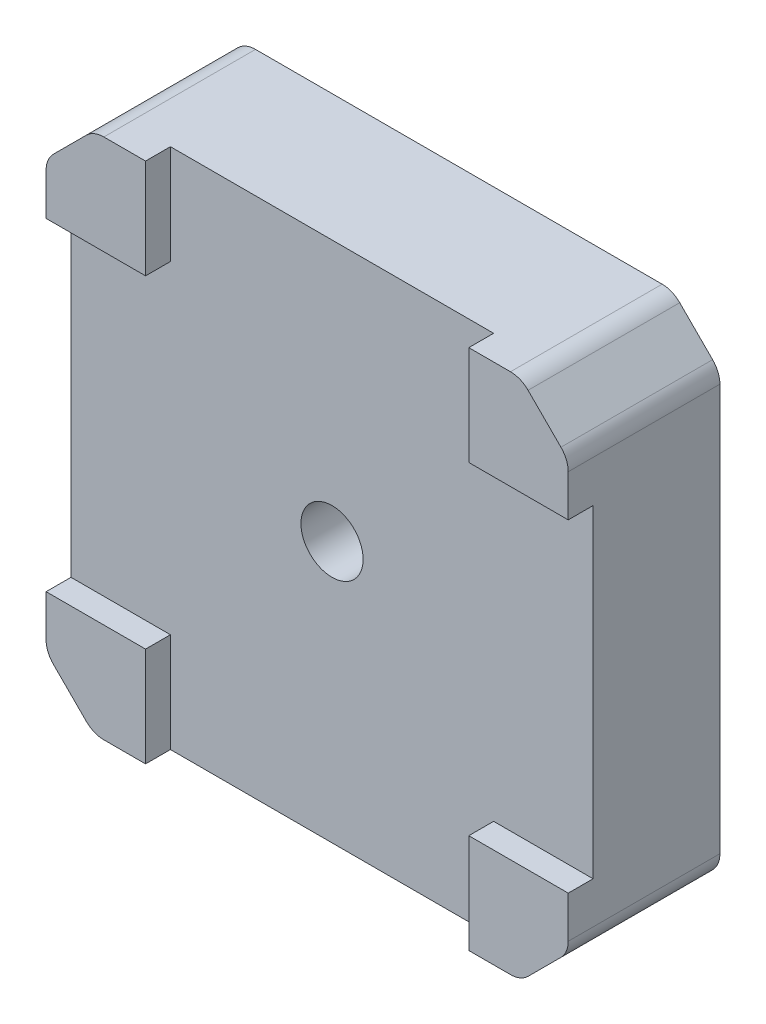
SolidWorks part; units mm, degrees
material "Alumina"
ref_plane "Front" through (0, 0, 0) normal (0, 0, 1) x (1, 0, 0)
ref_plane "Top" through (0, 0, 0) normal (0, 1, 0) x (1, 0, 0)
ref_plane "Right" through (0, 0, 0) normal (1, 0, 0) x (0, 0, -1)
sketch "Sketch1" plane through (0, 0, 0) normal (0, 0, 1) x (1, 0, 0)
  line L0 (-17.1838, 21) -> (-21, 17.1838)
  line L1 (-17.1838, -21) -> (17.1838, -21)
  line L2 (-21, -17.1838) -> (-21, 17.1838)
  line L3 (-17.1838, 21) -> (17.1838, 21)
  line L4 (21, -17.1838) -> (21, 17.1838)
  line L5 (-19.0919, 19.0919) -> (19.0919, -19.0919) construction
  line L6 (19.0919, 19.0919) -> (-19.0919, -19.0919) construction
  line L7 (0, -21) -> (0, 21) construction
  line L8 (-21, 0) -> (21, 0) construction
  line L9 (17.1838, 21) -> (21, 17.1838)
  line L10 (17.1838, -21) -> (21, -17.1838)
  line L11 (-17.1838, -21) -> (-21, -17.1838)
  point P0 (0, 0)
  dimension "D1" = 42
  dimension "D2" = 42
  dimension "D3" = 54
extrude "Boss-Extrude1" add sketch "Sketch1" along normal blind 12.2
sketch "Sketch2" plane through (21, 0, 0) normal (1, 0, 0) x (0, 0, -1)
  line L0 (-12.2, -17.1838) -> (-12.2, 17.1838) construction
  line L1 (-12.2, 13) -> (-10.2, 13)
  line L2 (-12.2, 13) -> (-12.2, -13)
  line L3 (-12.2, -13) -> (-10.2, -13)
  line L4 (-10.2, 13) -> (-10.2, -13)
  line L7 (0, 0) -> (-12.2, 0) construction
  line L8 (0, -17.1838) -> (0, 17.1838) construction
  dimension "D1" = 2
  dimension "D2" = 26
extrude "Cut-Extrude1" cut sketch "Sketch2" against normal through all
sketch "Sketch3" plane through (0, 21, 0) normal (0, 1, 0) x (1, 0, 0)
  line L0 (17.1838, -12.2) -> (-17.1838, -12.2) construction
  line L1 (-13, -12.2) -> (13, -12.2)
  line L2 (-13, -12.2) -> (-13, -10.2)
  line L3 (-13, -10.2) -> (13, -10.2)
  line L4 (13, -12.2) -> (13, -10.2)
  line L7 (0, 0) -> (0, -12.2) construction
  line L8 (17.1838, 0) -> (-17.1838, 0) construction
  dimension "D1" = 2
  dimension "D2" = 26
extrude "Cut-Extrude2" cut sketch "Sketch3" against normal through all
sketch "Sketch4" plane through (0, 0, 0) normal (0, 0, -1) x (-1, 0, 0)
  circle A0 centre (0, 0) radius 16.5
  dimension "D1" = 33
extrude "Cut-Extrude3" cut sketch "Sketch4" against normal blind 0.6
sketch "Sketch5" plane through (0, 0, 0.6) normal (0, 0, -1) x (-1, 0, 0)
  circle A0 centre (0, 0) radius 11
  dimension "D1" = 22
extrude "Boss-Extrude2" add sketch "Sketch5" along normal blind 2.6
sketch "Sketch6" plane through (0, 0, -2) normal (0, 0, -1) x (-1, 0, 0)
  circle A0 centre (0, 0) radius 3.25
  dimension "D1" = 6.5
extrude "Cut-Extrude4" cut sketch "Sketch6" against normal blind 2
sketch "Sketch7" plane through (0, 0, 0) normal (0, 0, -1) x (-1, 0, 0)
  circle A0 centre (0, 0) radius 2.5
  dimension "D1" = 5
extrude "Cut-Extrude5" cut sketch "Sketch7" against normal through all
fillet "Fillet1" radius 0.5 1 edges at (-3.25, 0, -2)
fillet "Fillet3" radius 0.5 1 edges at (-11, 0, 0.6)
fillet "Fillet4" radius 2 8 edges at (21, 17.1838, 6.1) (17.1838, 21, 6.1) (-17.1838, 21, 6.1) (-21, 17.1838, 6.1) (-21, -17.1838, 6.1) (-17.1838, -21, 6.1) (17.1838, -21, 6.1) (21, -17.1838, 6.1)
hole_wizard "M3x0.5 Tapped Hole1" positions "Sketch9" profile "Sketch8" tap size "M3x0.5" standard "ANSI Metric"
sketch "Sketch9" plane through (0, 0, 0) normal (0, 0, -1) x (-1, 0, 0)
  line L0 (0, 0) -> (-21, 0) construction
  line L1 (-21, -16.3553) -> (-21, 16.3553) construction
  line L2 (0, 0) -> (0, 21) construction
  line L3 (-16.3553, 21) -> (16.3553, 21) construction
  point P0 (-15.5, -15.5)
  point P9 (-15.5, 15.5)
  point P17 (15.5, 15.5)
  point P18 (15.5, -15.5)
  dimension "D1" = 31
  dimension "D2" = 31
sketch "Sketch8" plane through (15.5, -15.5, 0) normal (1, 0, 0) x (0, 1, 0)
  line L0 (0, 0) -> (0, 10.9013)
  line L1 (0, 10.9013) -> (1.5, 10)
  line L2 (1.5, 10) -> (1.5, 0.25)
  line L3 (1.5, 0.25) -> (1.75, 0)
  line L5 (1.75, 0) -> (0, 0)
  line L6 (-1.5, 0.25) -> (-1.75, 0) construction
  line L10 (0, 10.9013) -> (-1.5, 10) construction
  line L11 (0, -6.35) -> (0, 107.95) construction
  dimension "Tap Drill Dia." = 3
  dimension "Tap Drill Depth" = 10
  dimension "Near C'Sink Dia." = 3.5
  dimension "Near C'Sink Angle" = 90
  dimension "Drill Angle" = 118
